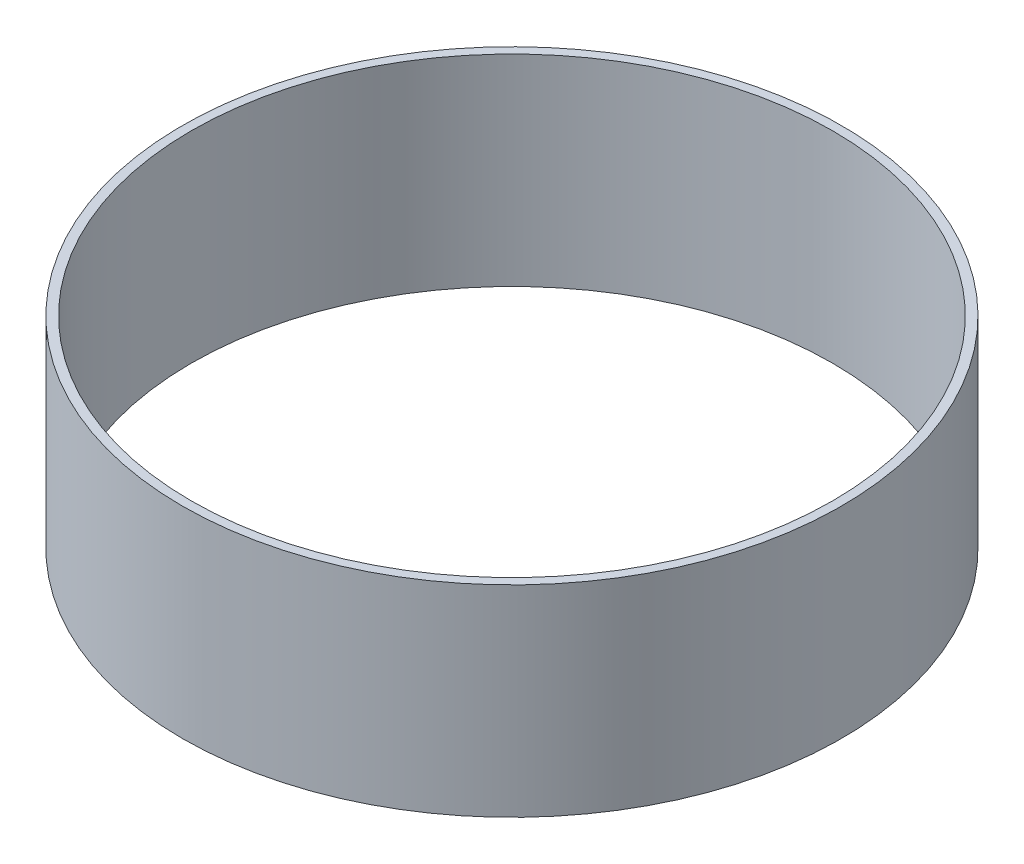
SolidWorks part; units mm, degrees
ref_plane "Front Plane" through (0, 0, 0) normal (0, 0, 1) x (1, 0, 0)
ref_plane "Top Plane" through (0, 0, 0) normal (0, 1, 0) x (1, 0, 0)
ref_plane "Right Plane" through (0, 0, 0) normal (1, 0, 0) x (0, 0, -1)
sketch "Sketch1" plane through (0, 0, 0) normal (0, 1, 0) x (1, 0, 0)
  circle A0 centre (0, 0) radius 43
  circle A1 centre (0, 0) radius 44.2
  dimension "D1" = 86
  dimension "D2" = 1.2
extrude "Boss-Extrude1" add sketch "Sketch1" along normal blind 27
